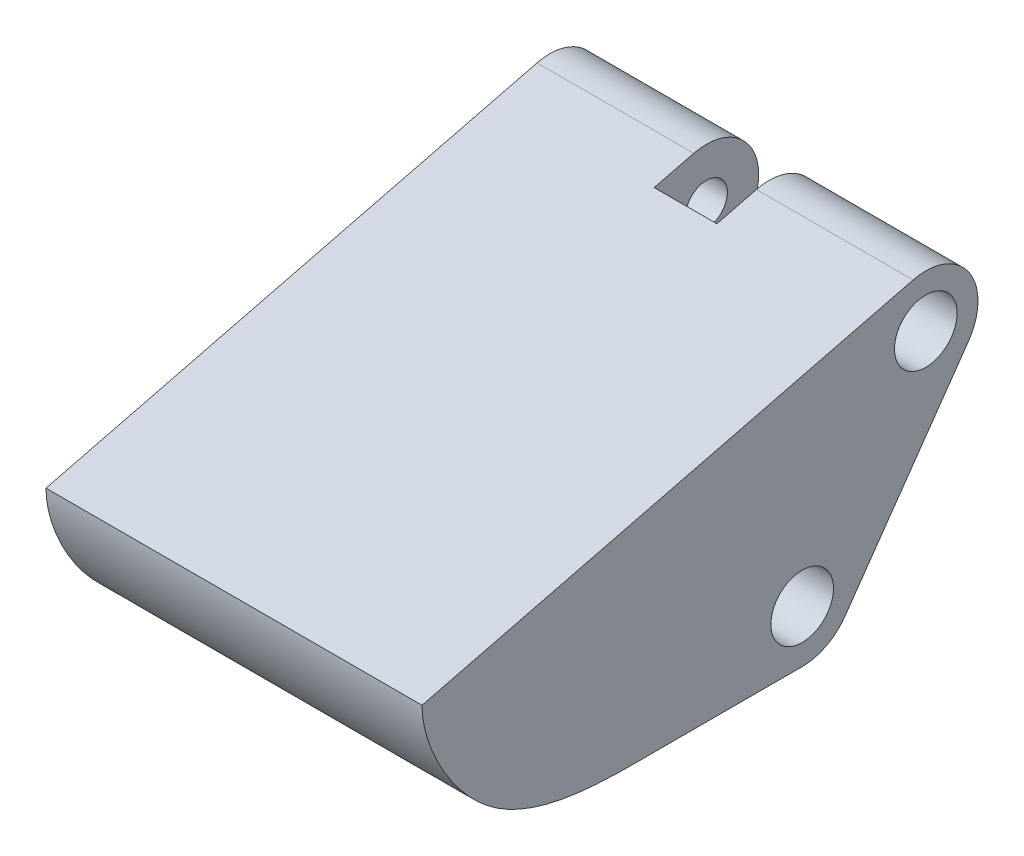
SolidWorks part; units mm, degrees
ref_plane "Front Plane" through (0, 0, 0) normal (0, 0, 1) x (1, 0, 0)
ref_plane "Top Plane" through (0, 0, 0) normal (0, 1, 0) x (1, 0, 0)
ref_plane "Right Plane" through (0, 0, 0) normal (1, 0, 0) x (0, 0, -1)
sketch "Sketch2" plane through (0, 0, 0) normal (1, 0, 0) x (0, 0, -1)
  line L0 (-6.4918, 5.8771) -> (-30, 0)
  line L1 (-18.5, -7.5) -> (-10.5, -7.5)
  line L5 (0, 7.5) -> (0, -7.5) construction
  line L6 (0, -7.5) -> (-10.5, -7.5) construction
  line L7 (-3.8374, 2.018) -> (-9.7536, -6.4337)
  line L8 (-11.8016, -7.5) -> (-18.5, -7.5)
  line L9 (-30, 0) -> (0, 0) construction
  arc A0 (-9.7536, -6.4337) -> (-11.8016, -7.5) centre (-11.8016, -5) cw
  arc A1 (-3.8374, 2.018) -> (-6.4918, 5.8771) centre (-5.8855, 3.4517) ccw
  circle A4 centre (-11.8016, -5) radius 1
  circle A5 centre (-5.8855, 3.4517) radius 1
  spline S0 degree 3 poles (-30, 0) (-30, -1.8251) (-26.8932, -7.806) (-20.7728, -7.5) (-18.5, -7.5) knots 0 0 0 0 0.460453 1 1 1 1
  point P0 (0, 0)
  point P13 (0, 0)
  dimension "D5" = 2.5
  dimension "D6" = 8
  dimension "D8" = 2
  dimension "D9" = 2
  dimension "D10" = 2.5
  dimension "D12" = 2.5
  dimension "D1" = 15
  dimension "D2" = 30
  dimension "D3" = 10.5
  dimension "D4" = 8
  dimension "D7" = 6
  dimension "D11" = 2.5
  dimension "D13" = 2.5
extrude "Boss-Extrude1" add sketch "Sketch2" along normal mid plane 18 contours L0 S0 L1 A0 L7 A1
ref_plane "Plane1" through (0, 5.9517, 0) normal (0, 1, 0) x (1, 0, 0)
sketch "Sketch4" plane through (0, 5.9517, 0) normal (0, 1, 0) x (1, 0, 0)
  line L0 (9, -3.3855) -> (-9, -3.3855) construction
  line L1 (1.5, -8.3855) -> (-1.5, -8.3855)
  line L2 (1.5, -8.3855) -> (1.5, -3.3855)
  line L3 (1.5, -3.3855) -> (-1.5, -3.3855)
  line L4 (-1.5, -8.3855) -> (-1.5, -3.3855)
  line L5 (1.5, -8.3855) -> (-1.5, -3.3855) construction
  line L6 (1.5, -3.3855) -> (-1.5, -8.3855) construction
  line L9 (-9, -4.9386) -> (9, -4.9386) construction
  line L10 (-9, -3.3855) -> (-9, -6.4918) construction
  line L11 (9, -6.4918) -> (9, -3.3855) construction
  point P0 (0, -5.8855)
  point P13 (0, -4.9386)
  dimension "D1" = 5
  dimension "D2" = 3
extrude "Cut-Extrude1" cut sketch "Sketch4" against normal blind 15
sketch "Sketch5" plane through (0, -7.5, 0) normal (0, -1, 0) x (1, 0, 0)
  line L0 (-3, 15.8016) -> (3, 15.8016)
  line L1 (3, 5.8016) -> (-3, 5.8016)
  line L2 (3, 5.8016) -> (3, 15.8016)
  line L4 (-3, 5.8016) -> (-3, 15.8016)
  line L5 (3, 5.8016) -> (-3, 15.8016) construction
  line L6 (3, 15.8016) -> (-3, 5.8016) construction
  line L7 (9, 11.8016) -> (-9, 11.8016) construction
  point P0 (0, 10.8016)
  dimension "D1" = 4
  dimension "D2" = 10
  dimension "D3" = 6
extrude "Cut-Extrude3" cut sketch "Sketch5" against normal blind 5.25
sketch "Sketch6" plane through (9, 0, 0) normal (1, 0, 0) x (0, 0, -1)
  circle A0 centre (-5.8855, 3.4517) radius 1.5
  circle A1 centre (-11.8016, -5) radius 1.5
  dimension "D1" = 3
extrude "Cut-Extrude4" cut sketch "Sketch6" against normal blind 3
sketch "Sketch7" plane through (-9, 0, 0) normal (-1, 0, 0) x (0, 0, 1)
  circle A0 centre (5.8855, 3.4517) radius 1.5
  circle A1 centre (11.8016, -5) radius 1.5
  dimension "D1" = 3
extrude "Cut-Extrude5" cut sketch "Sketch7" against normal blind 3
